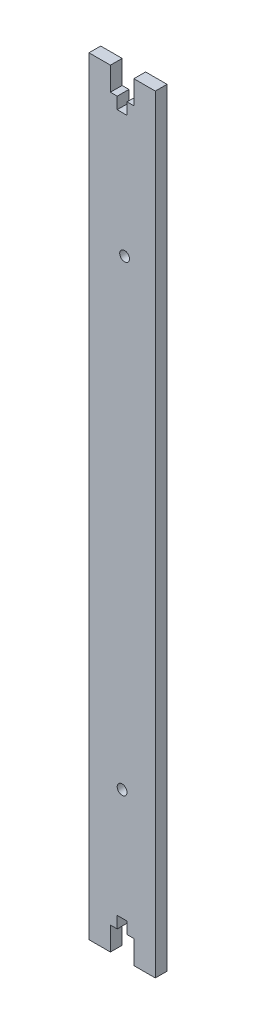
SolidWorks part; units mm, degrees
ref_plane "Front Plane" through (0, 0, 0) normal (0, 0, 1) x (1, 0, 0)
ref_plane "Top Plane" through (0, 0, 0) normal (0, 1, 0) x (1, 0, 0)
ref_plane "Right Plane" through (0, 0, 0) normal (1, 0, 0) x (0, 0, -1)
sketch "Sketch1" plane through (0, 0, 0) normal (0, 0, 1) x (1, 0, 0)
  line L1 (-14.14, 163.75) -> (14.14, 163.75)
  line L2 (-14.14, 163.75) -> (-14.14, -163.75)
  line L3 (-14.14, -163.75) -> (14.14, -163.75)
  line L4 (14.14, 163.75) -> (14.14, -163.75)
  line L5 (-14.14, 163.75) -> (14.14, -163.75) construction
  line L6 (-14.14, -163.75) -> (14.14, 163.75) construction
  point P0 (0, 0)
  dimension "D1" = 327.5
  dimension "D2" = 28.28
extrude "Boss-Extrude1" add sketch "Sketch1" along normal blind 5
sketch "Sketch2" plane through (0, 0, 5) normal (0, 0, 1) x (1, 0, 0)
  line L0 (0, 163.75) -> (0, 146.4815) construction
  line L1 (14.14, 163.75) -> (-14.14, 163.75) construction
  line L2 (0, 0) -> (-9.143, 0) construction
  line L3 (5, 163.75) -> (5, 153.75)
  line L4 (5, 153.75) -> (2.1, 153.75)
  line L5 (2.1, 153.75) -> (2.1, 148.75)
  line L6 (-2.1, 153.75) -> (-2.1, 148.75)
  line L7 (-5, 153.75) -> (-2.1, 153.75)
  line L8 (-5, 163.75) -> (-5, 153.75)
  line L9 (-5, 163.75) -> (5, 163.75)
  line L10 (2.1, 148.75) -> (-2.1, 148.75)
  line L11 (2.1, -148.75) -> (-2.1, -148.75)
  line L12 (-5, -163.75) -> (5, -163.75)
  line L13 (-5, -163.75) -> (-5, -153.75)
  line L14 (-5, -153.75) -> (-2.1, -153.75)
  line L15 (-2.1, -153.75) -> (-2.1, -148.75)
  line L16 (2.1, -153.75) -> (2.1, -148.75)
  line L17 (5, -153.75) -> (2.1, -153.75)
  line L18 (5, -163.75) -> (5, -153.75)
  line L19 (-16.2656, 96.25) -> (18.3826, 96.25) construction
  line L20 (-16.2656, 93.75) -> (-16.2656, 98.75) construction
  circle A0 centre (1.0585, 96.25) radius 2.1
  dimension "D5" = 4.2
  dimension "D1" = 10
  dimension "D2" = 2.9
  dimension "D3" = 5
  dimension "D4" = 5
extrude "Cut-Extrude1" cut sketch "Sketch2" against normal blind 10
sketch "Sketch3" plane through (0, 0, 5) normal (0, 0, 1) x (1, 0, 0)
  line L0 (-14.1443, -101.25) -> (14.14, -101.25) construction
  line L1 (-14.1443, -103.75) -> (-14.1443, -98.75) construction
  line L2 (14.14, -103.75) -> (14.14, -98.75) construction
  circle A0 centre (-0.0021, -101.25) radius 2.1
  dimension "D1" = 4.2
extrude "Cut-Extrude2" cut sketch "Sketch3" against normal blind 10
